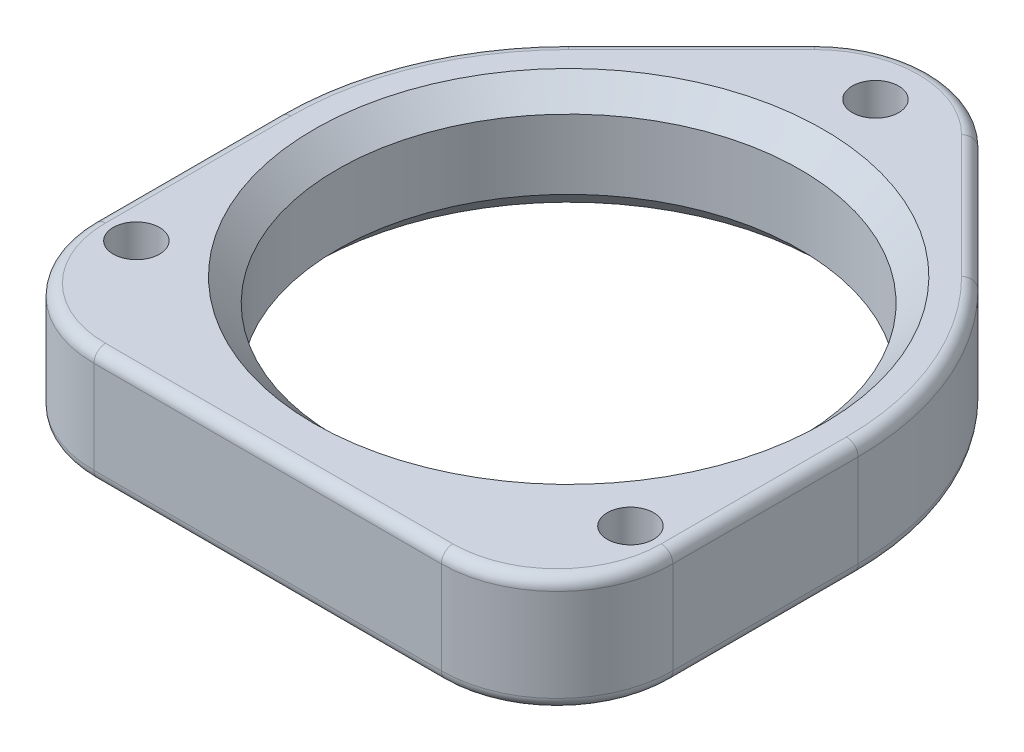
SolidWorks part; units mm, degrees
ref_plane "Front Plane" through (0, 0, 0) normal (0, 0, 1) x (1, 0, 0)
ref_plane "Top Plane" through (0, 0, 0) normal (0, 1, 0) x (1, 0, 0)
ref_plane "Right Plane" through (0, 0, 0) normal (1, 0, 0) x (0, 0, -1)
sketch "Sketch1" plane through (0, 0, 0) normal (0, 1, 0) x (1, 0, 0)
  circle A0 centre (0, 0) radius 20
  circle A1 centre (0, 0) radius 25
  dimension "D1" = 40
  dimension "D2" = 5
extrude "Boss-Extrude1" add sketch "Sketch1" along normal blind 10
sketch "Sketch3" plane through (0, 10, 0) normal (0, 1, 0) x (1, 0, 0)
  line L0 (-25, -26) -> (25, -26)
  line L1 (-25, 0) -> (-25, -26) construction
  line L2 (25, 0) -> (25, -26) construction
  line L3 (-25, 0) -> (-25, -26)
  line L4 (25, 0) -> (25, -26)
  arc A0 (-25, 0) -> (25, 0) centre (0, 0) ccw
  point P6 (0, -26)
  dimension "D1" = 50
  dimension "D2" = 26
extrude "Boss-Extrude2" add sketch "Sketch3" against normal blind 10
sketch "Sketch2" plane through (0, 10, 0) normal (0, 1, 0) x (1, 0, 0)
  line L0 (0, 0) -> (0, 26.5) construction
  line L1 (-21.335, -16) -> (21.335, -16) construction
  circle A0 centre (-21.335, -16) radius 2
  circle A1 centre (0, 26.5) radius 2
  circle A2 centre (21.335, -16) radius 2
  point P5 (0, -16)
  dimension "D4" = 4
  dimension "D1" = 26.5
  dimension "D2" = 42.67
  dimension "D3" = 16
sketch "Sketch4" plane through (0, 10, 0) normal (0, 1, 0) x (1, 0, 0)
  line L0 (0, 0) -> (25, 0) construction
  line L1 (0, 0) -> (17.6777, 17.6777) construction
  line L2 (0, 0) -> (-17.6777, 17.6777) construction
  line L3 (-17.6777, 17.6777) -> (0, 35.3553)
  line L4 (0, 35.3553) -> (17.6777, 17.6777)
  arc A0 (25, 0) -> (-25, 0) centre (0, 0) ccw construction
  arc A1 (25, 0) -> (-17.6777, 17.6777) centre (0, 0) ccw
  arc M1 (25, 0) -> (-25, 0) centre (0, 0) ccw
extrude "Boss-Extrude3" add sketch "Sketch4" against normal blind 10 contours L4 L3 M1
fillet "Fillet1" radius 10 1 edges at (0, 5, -35.3553)
extrude "Cut-Extrude1" cut sketch "Sketch2" against normal blind 10
chamfer "Chamfer1" distance 2 angle 45 1 edges at (0, 0, 20)
fillet "Fillet2" radius 10 2 edges at (25, 5, 26) (-25, 5, 26)
chamfer "Chamfer2" distance 2 angle 45 1 edges at (0, 10, 20)
fillet "Fillet3" radius 1 20 edges at (-22.0711, 0, 23.0711) (-22.0711, 10, 23.0711) (-25, 0, 8) (-25, 10, 8) (-23.097, 10, -9.5671) (-23.097, 0, -9.5671) (-12.3744, 0, -22.981) (0, 0, -31.2132) (0, 10, -31.2132) (12.3744, 0, -22.981) (23.097, 10, -9.5671) (23.097, 0, -9.5671) (25, 10, 8) (25, 0, 8) (22.0711, 0, 23.0711) (22.0711, 10, 23.0711) (0, 0, 26) (0, 10, 26) (12.3744, 10, -22.981) (-12.3744, 10, -22.981)
